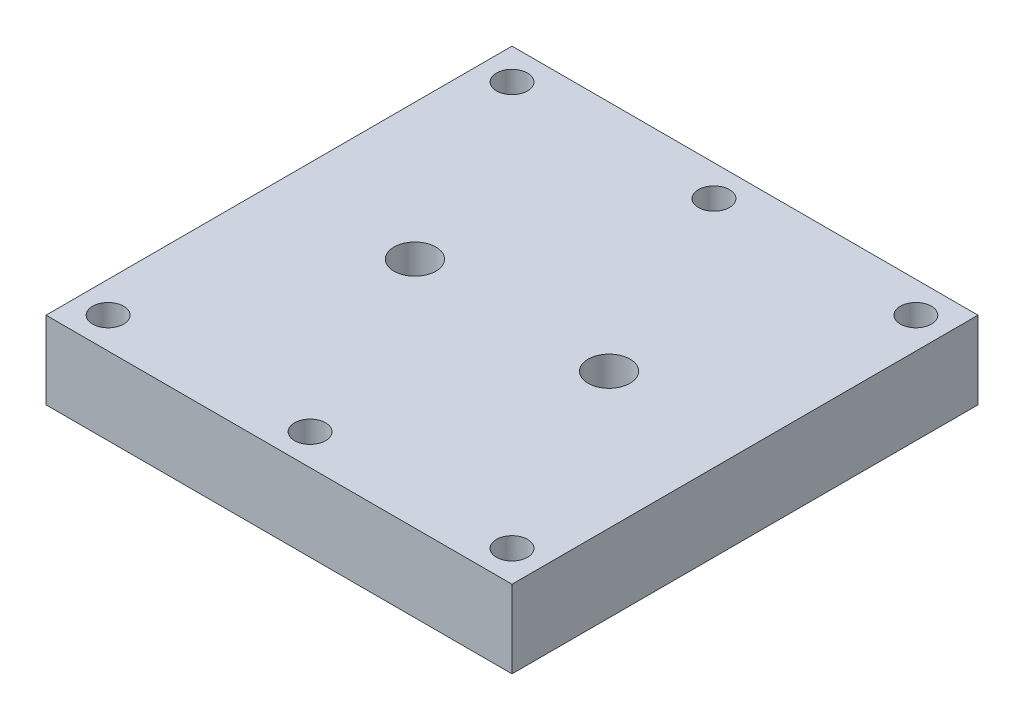
SolidWorks part; units mm, degrees
ref_plane "Front Plane" through (0, 0, 0) normal (0, 0, 1) x (1, 0, 0)
ref_plane "Top Plane" through (0, 0, 0) normal (0, 1, 0) x (1, 0, 0)
ref_plane "Right Plane" through (0, 0, 0) normal (1, 0, 0) x (0, 0, -1)
sketch "Sketch2" plane through (0, 0, 0) normal (0, 1, 0) x (1, 0, 0)
  line L1 (30, -30) -> (-30, -30)
  line L2 (30, -30) -> (30, 30)
  line L3 (30, 30) -> (-30, 30)
  line L4 (-30, -30) -> (-30, 30)
  line L5 (30, -30) -> (-30, 30) construction
  line L6 (30, 30) -> (-30, -30) construction
  point P0 (0, 0)
  dimension "D1" = 60
  dimension "D2" = 60
extrude "Boss-Extrude1" add sketch "Sketch2" along normal blind 10
sketch "Sketch3" plane through (0, 10, 0) normal (0, 1, 0) x (1, 0, 0)
  line L0 (30, 30) -> (-30, 30) construction
  line L1 (-30, 30) -> (-30, -30) construction
  line L2 (30, -30) -> (30, 30) construction
  line L4 (-30, -30) -> (30, -30) construction
  circle A0 centre (-26, 26) radius 2
  circle A1 centre (-26, -26) radius 2
  circle A2 centre (0, -26) radius 2
  circle A3 centre (26, -26) radius 2
  circle A4 centre (26, 26) radius 2
  circle A5 centre (0, 26) radius 2
  point P18 (0, -30)
  dimension "D1" = 4
  dimension "D2" = 4
  dimension "D3" = 4
  dimension "D4" = 4
  dimension "D5" = 4
  dimension "D6" = 4
  dimension "D7" = 4
  dimension "D8" = 4
  dimension "D9" = 4
  dimension "D10" = 4
  dimension "D11" = 4
  dimension "D12" = 4
  dimension "D13" = 4
  dimension "D14" = 4
  dimension "D15" = 4
  dimension "D16" = 4
extrude "Cut-Extrude1" cut sketch "Sketch3" against normal blind 10
sketch "Sketch4" plane through (0, 0, 0) normal (0, -1, 0) x (1, 0, 0)
  circle A0 centre (0, 0) radius 6.35
  dimension "D1" = 12.7
extrude "Cut-Extrude2" cut sketch "Sketch4" against normal blind 3.2
sketch "Sketch5" plane through (0, 10, 0) normal (0, 1, 0) x (1, 0, 0)
  circle A0 centre (12.5, 0) radius 2.7
  circle A1 centre (-12.5, 0) radius 2.7
  dimension "D1" = 5.4
  dimension "D2" = 5.4
  dimension "D3" = 25
  dimension "D4" = 12.5
extrude "Cut-Extrude3" cut sketch "Sketch5" against normal blind 7
sketch "Sketch6" plane through (0, 0, 0) normal (0, -1, 0) x (1, 0, 0)
  circle A0 centre (12.5, 0) radius 0.5
  circle A1 centre (-12.5, 0) radius 0.5
  dimension "D1" = 1
  dimension "D2" = 1
extrude "Cut-Extrude4" cut sketch "Sketch6" against normal blind 3
